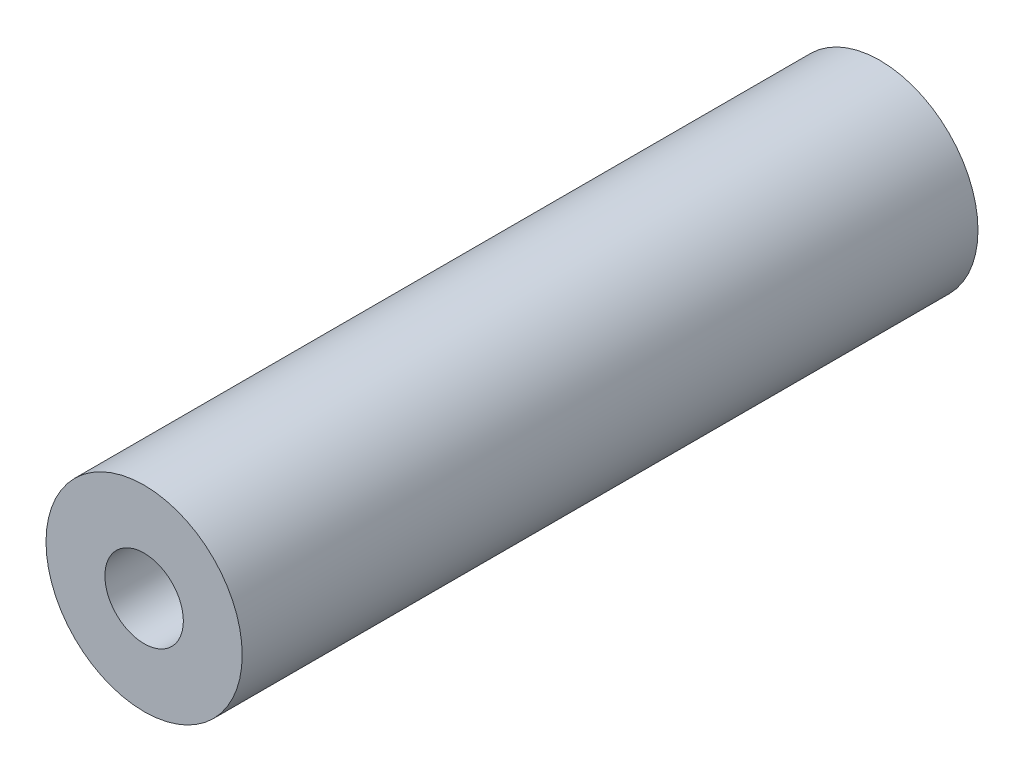
SolidWorks part; units mm, degrees
ref_plane "Front Plane" through (0, 0, 0) normal (0, 0, 1) x (1, 0, 0)
ref_plane "Top Plane" through (0, 0, 0) normal (0, 1, 0) x (1, 0, 0)
ref_plane "Right Plane" through (0, 0, 0) normal (1, 0, 0) x (0, 0, -1)
sketch "Sketch1" plane through (0, 0, 0) normal (0, 0, 1) x (1, 0, 0)
  circle A0 centre (0, 0) radius 2
  circle A1 centre (0, 0) radius 5
  dimension "D1" = 4
  dimension "D2" = 10
extrude "Boss-Extrude1" add sketch "Sketch1" along normal mid plane 37.5
